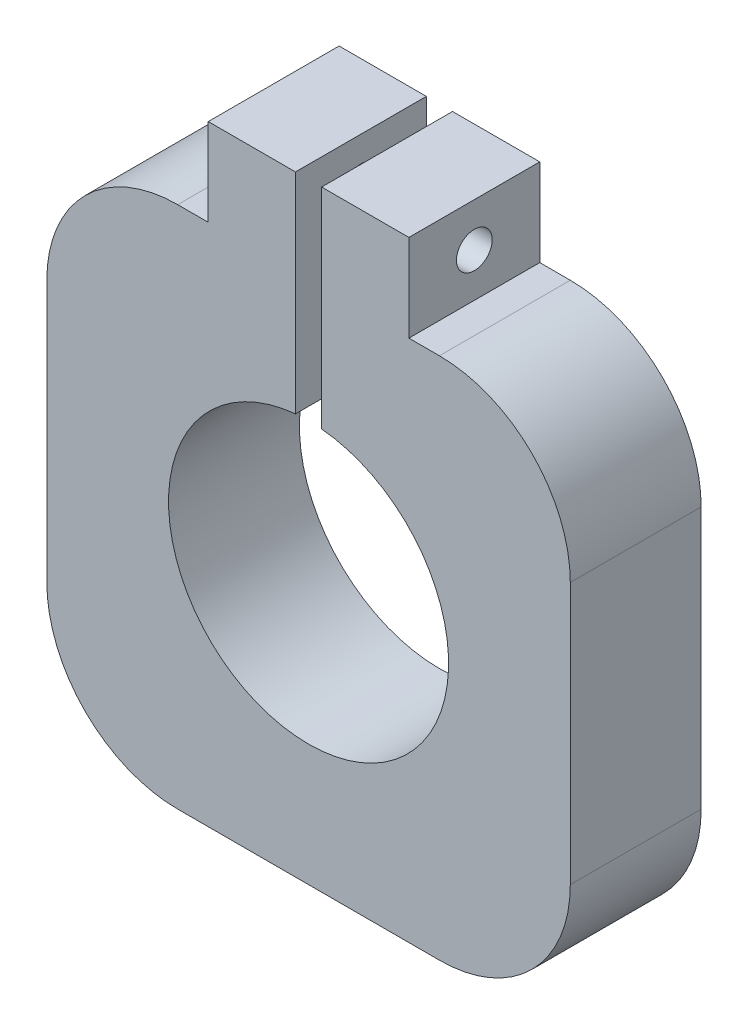
SolidWorks part; units mm, degrees
ref_plane "Front Plane" through (0, 0, 0) normal (0, 0, 1) x (1, 0, 0)
ref_plane "Top Plane" through (0, 0, 0) normal (0, 1, 0) x (1, 0, 0)
ref_plane "Right Plane" through (0, 0, 0) normal (1, 0, 0) x (0, 0, -1)
sketch "Sketch3" plane through (0, 0, 0) normal (0, 0, 1) x (1, 0, 0)
  line L0 (-1.5, 40) -> (-1.5, 15.9798)
  line L1 (30, -30) -> (-30, -30)
  line L2 (30, -30) -> (30, 30)
  line L3 (30, 30) -> (11.5, 30)
  line L4 (-30, -30) -> (-30, 30)
  line L5 (30, -30) -> (-30, 30) construction
  line L6 (30, 30) -> (-30, -30) construction
  line L7 (-1.5, 30) -> (-1.5, 15.9798) construction
  line L10 (-1.5, 40) -> (-11.5, 40)
  line L11 (-11.5, 30) -> (-11.5, 40)
  line L13 (1.5, 30) -> (1.5, 40)
  line L14 (1.5, 40) -> (11.5, 40)
  line L15 (11.5, 30) -> (11.5, 40)
  line L16 (1.5, 30) -> (1.5, 15.9798) construction
  line L17 (-11.5, 30) -> (-30, 30)
  line L18 (1.5, 30) -> (1.5, 15.9798)
  arc A0 (-1.5, 15.9798) -> (1.5, 15.9798) centre (0, 0) ccw
  point P12 (0, 30)
  dimension "D1" = 60
  dimension "D3" = 32.1
  dimension "D2" = 60
  dimension "D4" = 10
  dimension "D5" = 3
  dimension "D6" = 10
  dimension "D7" = 10
  dimension "D8" = 10
extrude "Boss-Extrude2" add sketch "Sketch3" along normal blind 15
fillet "Fillet5" radius 15 1 edges at (30, 30, 7.5)
fillet "Fillet6" radius 15 1 edges at (-30, 30, 7.5)
fillet "Fillet7" radius 15 1 edges at (-30, -30, 7.5)
fillet "Fillet8" radius 15 1 edges at (30, -30, 7.5)
sketch "Sketch4" plane through (11.5, 0, 0) normal (1, 0, 0) x (0, 0, -1)
  line L0 (0, 40) -> (-15, 30) construction
  line L1 (-15, 40) -> (0, 30) construction
  circle A0 centre (-7.5, 35) radius 2.05
  dimension "D1" = 4.1
extrude "Cut-Extrude2" cut sketch "Sketch4" against normal up to surface (23 mm away) up to face at (-11.5, 35, 7.5)
